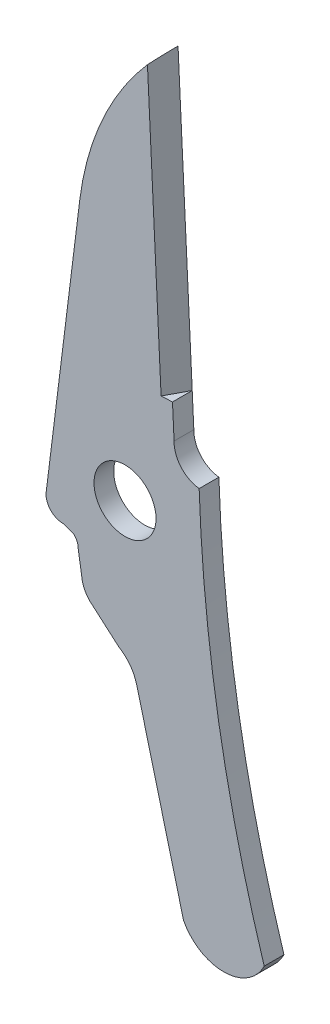
SolidWorks part; units mm, degrees
material "AISI 4340 Steel, normalized"
ref_plane "Front Plane" through (0, 0, 0) normal (0, 0, 1) x (1, 0, 0)
ref_plane "Top Plane" through (0, 0, 0) normal (0, 1, 0) x (1, 0, 0)
ref_plane "Right Plane" through (0, 0, 0) normal (1, 0, 0) x (0, 0, -1)
sketch "Sketch1" plane through (0, 0, 0) normal (0, 0, 1) x (1, 0, 0)
  line L0 (-34.2684, 6.7209) -> (42.5577, -21.2415) construction
  line L1 (9.0028, 22.7269) -> (9.714, 8.1219)
  line L2 (8.0312, -2.2288) -> (10.1398, -10.3568)
  line L3 (6.0508, -0.1312) -> (7.2192, -1.1472)
  line L4 (5.3967, 1.7698) -> (5.5522, 0.7792)
  line L5 (4.71, 2.4048) -> (5.1926, 2.2366)
  line L6 (5.4677, 15.404) -> (3.9622, 3.3136)
  arc A0 (9.714, 8.1219) -> (10.8427, 6.8322) centre (10.9838, 8.0944) ccw
  arc A1 (10.8427, 6.8322) -> (13.7722, -10.3288) centre (75.322, 9.0088) ccw
  arc A3 (13.7722, -10.3288) -> (10.1398, -10.3568) centre (11.949, -9.4316) cw
  arc A4 (8.0312, -2.2288) -> (7.2192, -1.1472) centre (6.3102, -2.6752) ccw
  arc A5 (5.5522, 0.7792) -> (6.0508, -0.1312) centre (6.8182, 0.8808) ccw
  arc A6 (5.1926, 2.2366) -> (5.3967, 1.7698) centre (4.7608, 1.7698) cw
  arc A7 (3.9622, 3.3136) -> (4.71, 2.4048) centre (4.71, 3.1668) ccw
  arc A8 (9.0028, 22.7269) -> (5.4677, 15.404) centre (18.0704, 13.8348) ccw
  circle A9 centre (7.504, 4.6908) radius 1.397
  dimension "D1" = 2.794
  dimension "D3" = 2.921
  dimension "D5" = 7.366
  dimension "D6" = 14.1224
  dimension "D9" = 2.794
  dimension "D12" = 1.1938
  dimension "D13" = 4.445
  dimension "D14" = 3.4798
  dimension "D15" = 10.5664
  dimension "D8" = 9.144
  dimension "D16" = 0.762
  dimension "D18" = 1.778
  dimension "D19" = 2.032
  dimension "D22" = 12.0904
  dimension "D23" = 14.605
  dimension "D25" = 67.818
  dimension "D27" = 64.516
  dimension "D28" = 8.128
  dimension "D30" = 1.1684
  dimension "D31" = 0.9906
  dimension "D33" = 2.286
  dimension "D7" = 3.4036
  dimension "D10" = 2.7432
  dimension "D11" = 0.6858
  dimension "D17" = 1.27
  dimension "D20" = 1.27
  dimension "D21" = 12.7
  dimension "D26" = 4.318
  dimension "D2" = 1.524
  dimension "D4" = 3.81
  dimension "D24" = 0.7112
  dimension "D29" = 1.016
  dimension "D32" = 0.4826
extrude "Boss-Extrude1" add sketch "Sketch1" along normal mid plane 0.889
ref_plane "Plane1" through (-1.2471, 25.6091, 0) normal (-0.0486, 0.9988, 0) x (0.9988, 0.0486, 0)
sketch "Sketch2" plane through (-1.2471, 25.6091, 0) normal (-0.0486, 0.9988, 0) x (0.9988, 0.0486, 0)
  line L0 (10.0976, 0.4445) -> (10.0976, -0.4445)
  line L1 (10.0976, -0.4445) -> (9.5843, -0.4445)
  line L2 (9.5843, -0.4445) -> (10.0976, 0.4445)
  dimension "D1" = 30
extrude "Cut-Extrude4" cut sketch "Sketch2" against normal blind 16.51
